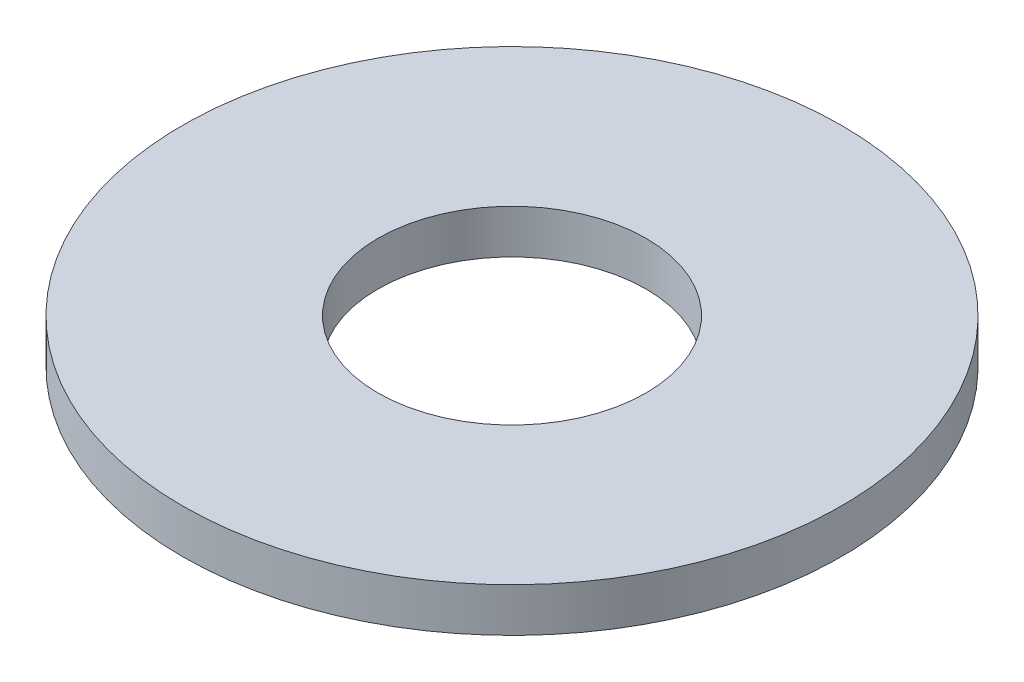
SolidWorks part; units mm, degrees
ref_plane "Front Plane" through (0, 0, 0) normal (0, 0, 1) x (1, 0, 0)
ref_plane "Top Plane" through (0, 0, 0) normal (0, 1, 0) x (1, 0, 0)
ref_plane "Right Plane" through (0, 0, 0) normal (1, 0, 0) x (0, 0, -1)
sketch "Sketch1" plane through (0, 0, 0) normal (0, 1, 0) x (1, 0, 0)
  circle A0 centre (0, 0) radius 7.5
  circle A1 centre (0, 0) radius 3.05
  dimension "D1" = 15
  dimension "D2" = 6.1
extrude "Boss-Extrude1" add sketch "Sketch1" along normal blind 1
